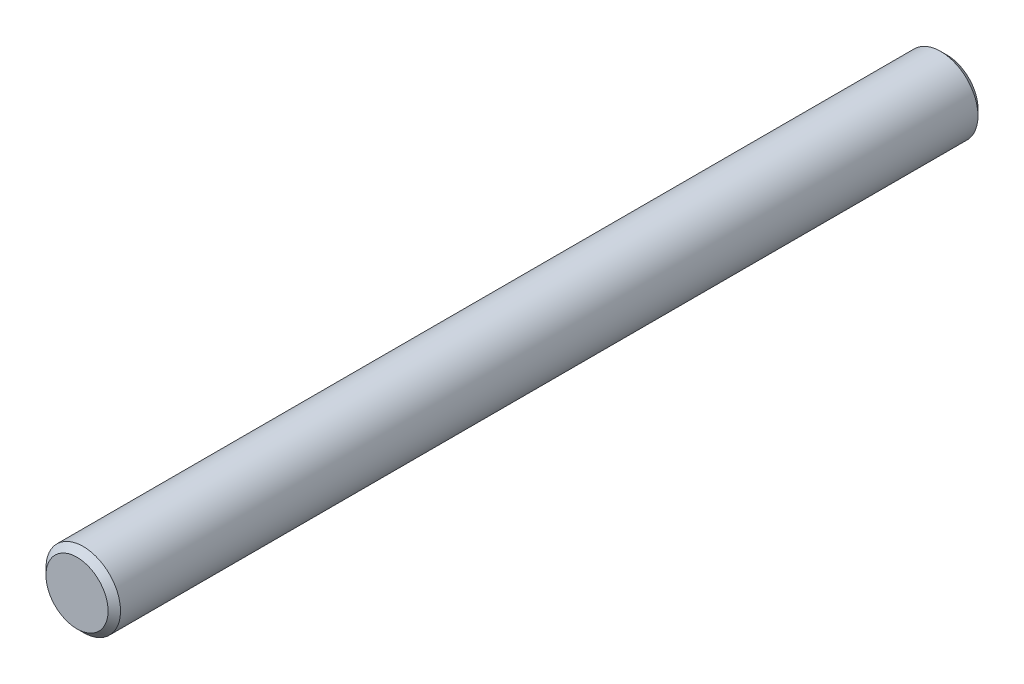
SolidWorks part; units mm, degrees
ref_plane "Plan de face" through (0, 0, 0) normal (0, 0, 1) x (1, 0, 0)
ref_plane "Plan de dessus" through (0, 0, 0) normal (0, 1, 0) x (1, 0, 0)
ref_plane "Plan de droite" through (0, 0, 0) normal (1, 0, 0) x (0, 0, -1)
sketch "Esquisse1" plane through (0, 0, 0) normal (0, 0, 1) x (1, 0, 0)
  circle A0 centre (0, 0) radius 3
  dimension "D1" = 6
extrude "Boss.-Extru.1" add sketch "Esquisse1" along normal blind 70
chamfer "Chanfrein1" distance 0.5 angle 45 2 edges at (3, 0, 0) (3, 0, 70)
